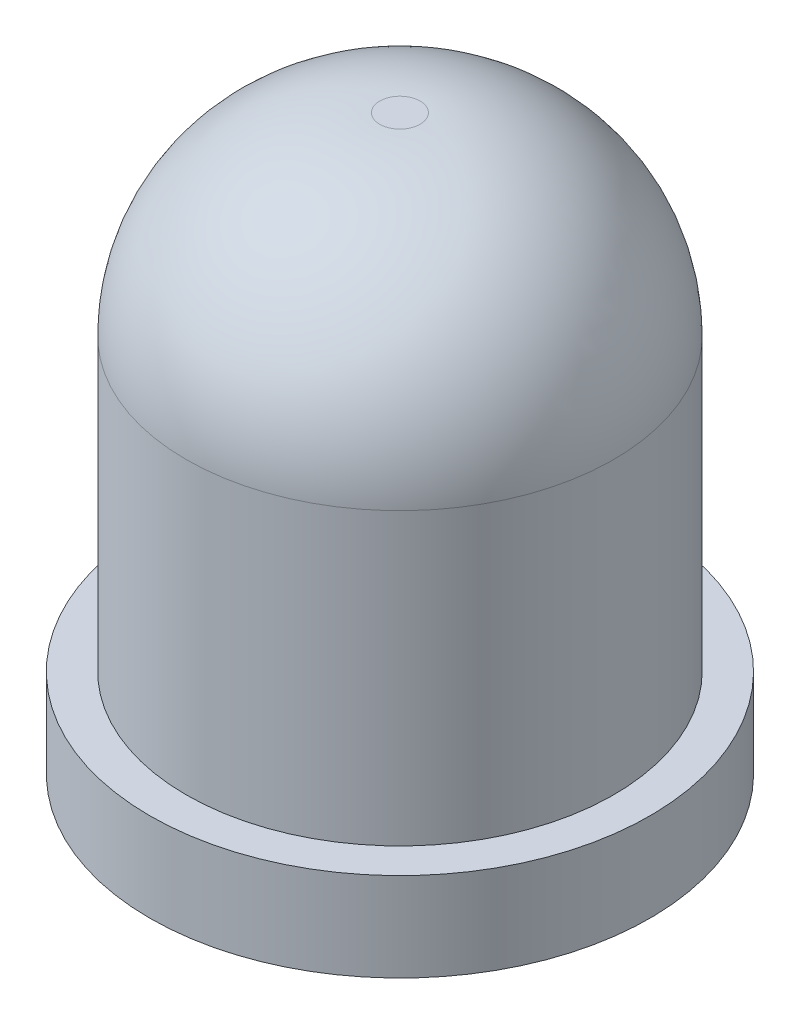
SolidWorks part; units mm, degrees
ref_plane "Plan de face" through (0, 0, 0) normal (0, 0, 1) x (1, 0, 0)
ref_plane "Plan de dessus" through (0, 0, 0) normal (0, 1, 0) x (1, 0, 0)
ref_plane "Plan de droite" through (0, 0, 0) normal (1, 0, 0) x (0, 0, -1)
sketch "Esquisse1" plane through (0, 0, 0) normal (0, 1, 0) x (1, 0, 0)
  circle A0 centre (0, 0) radius 3.1
  dimension "D1" = 6.2
extrude "Extrusion1" add sketch "Esquisse1" along normal blind 1.1
sketch "Esquisse2" plane through (0, 1.1, 0) normal (0, 1, 0) x (1, 0, 0)
  circle A0 centre (0, 0) radius 2.65
  dimension "D1" = 5.3
extrude "Extrusion2" add sketch "Esquisse2" along normal blind 6
fillet "Congé1" radius 2.4 1 edges at (0, 7.1, 2.65)
